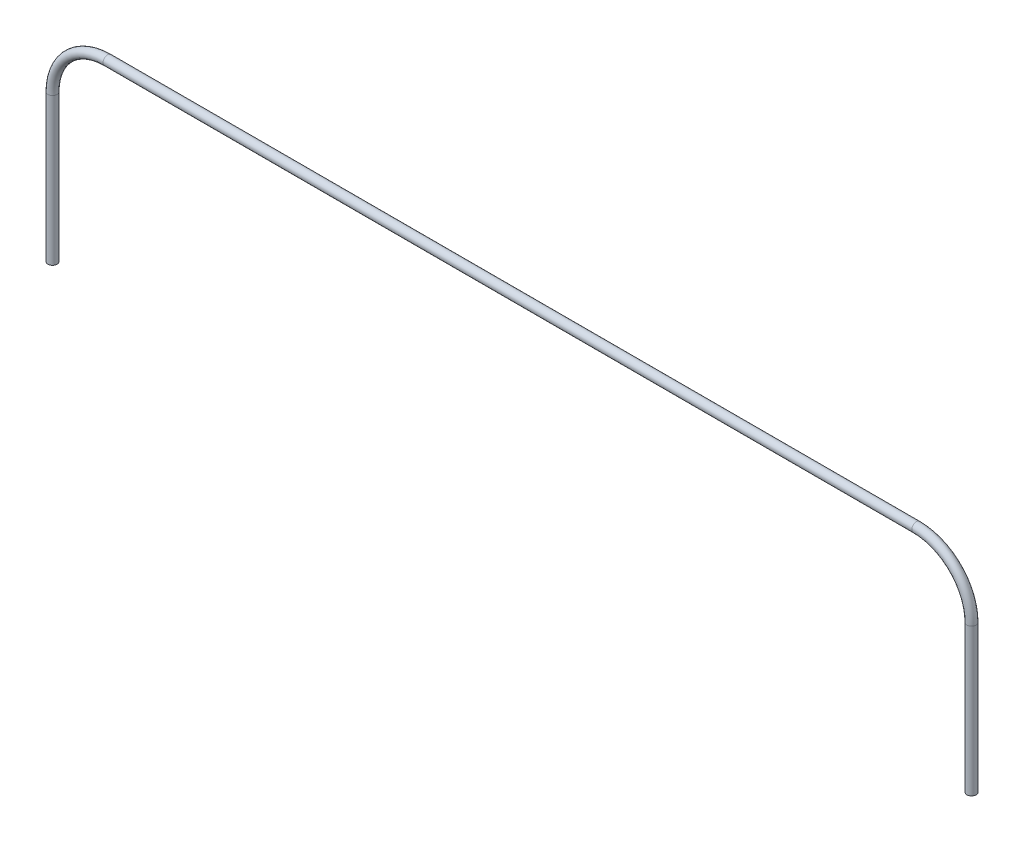
SolidWorks part; units mm, degrees
ref_plane "Plan de face" through (0, 0, 0) normal (0, 0, 1) x (1, 0, 0)
ref_plane "Plan de dessus" through (0, 0, 0) normal (0, 1, 0) x (1, 0, 0)
ref_plane "Plan de droite" through (0, 0, 0) normal (1, 0, 0) x (0, 0, -1)
sketch "Esquisse1" plane through (0, 0, 0) normal (0, 0, 1) x (1, 0, 0)
  line L0 (0, 0) -> (0, 8)
  line L1 (3, 11) -> (47, 11)
  line L2 (50, 8) -> (50, 0)
  arc A0 (0, 8) -> (3, 11) centre (3, 8) cw
  arc A1 (47, 11) -> (50, 8) centre (47, 8) cw
  dimension "D1" = 3
sketch "Esquisse4" plane through (0, 0, 0) normal (0, 1, 0) x (1, 0, 0)
  circle A0 centre (0, 0) radius 0.25
sweep "Balayage1" add profiles "Esquisse4" path "Esquisse1"
